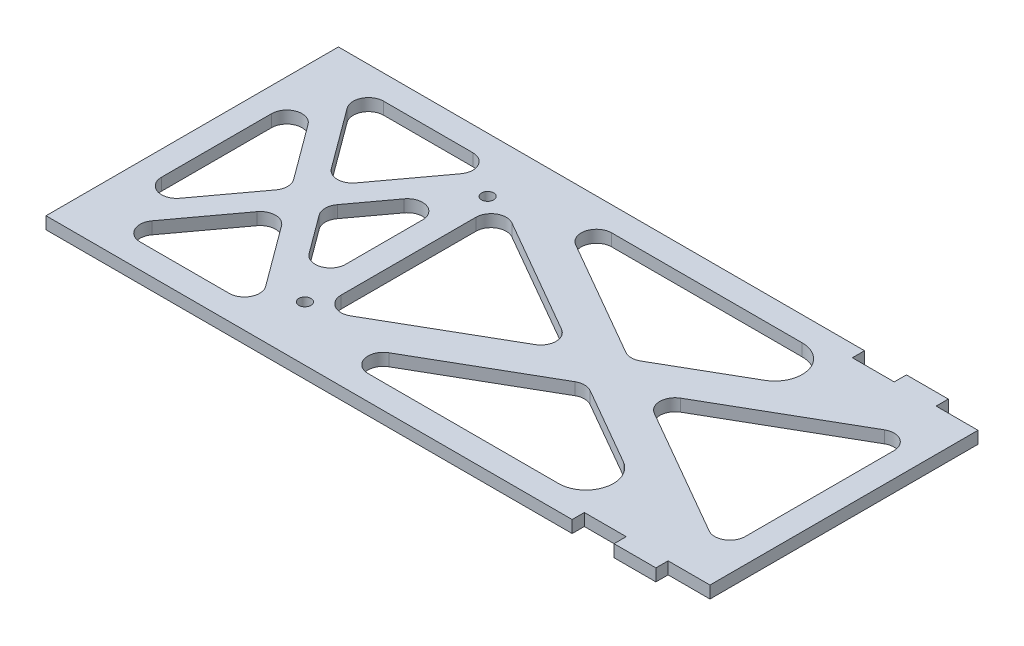
SolidWorks part; units mm, degrees
material "Beech"
ref_plane "Front Plane" through (0, 0, 0) normal (0, 0, 1) x (1, 0, 0)
ref_plane "Top Plane" through (0, 0, 0) normal (0, 1, 0) x (1, 0, 0)
ref_plane "Right Plane" through (0, 0, 0) normal (1, 0, 0) x (0, 0, -1)
sketch "Sketch1" plane through (0, 0, 0) normal (0, 1, 0) x (1, 0, 0)
  line L0 (-50.8, 60.96) -> (-50.8, -60.96) construction
  line L1 (135.89, 60.96) -> (-135.89, 60.96)
  line L2 (135.89, 60.96) -> (135.89, -60.96)
  line L3 (135.89, -60.96) -> (-135.89, -60.96)
  line L4 (-135.89, 60.96) -> (-135.89, -60.96)
  line L5 (135.89, 60.96) -> (-135.89, -60.96) construction
  line L6 (135.89, -60.96) -> (-135.89, 60.96) construction
  line L7 (0, 0) -> (-135.89, 0) construction
  line L8 (125.73, 50.8) -> (-125.73, 50.8)
  line L9 (-125.73, 50.8) -> (-125.73, -50.8)
  line L10 (125.73, -50.8) -> (-125.73, -50.8)
  line L11 (125.73, 50.8) -> (125.73, -50.8)
  line L12 (50.8, 60.96) -> (50.8, -60.96) construction
  line L13 (-125.73, 50.8) -> (-50.8, -50.8) construction
  line L14 (-125.73, -50.8) -> (-50.8, 50.8) construction
  line L15 (-50.8, 50.8) -> (50.8, -50.8) construction
  line L16 (-50.8, -50.8) -> (50.8, 50.8) construction
  line L17 (50.8, 50.8) -> (125.73, -50.8) construction
  line L18 (50.8, -50.8) -> (125.73, 50.8) construction
  line L19 (-125.73, 42.2412) -> (-57.1121, -50.8)
  line L20 (-50.8, 50.8) -> (125.73, -50.8) construction
  line L21 (-50.8, -50.8) -> (125.73, 50.8) construction
  line L22 (-119.4179, -50.8) -> (-53.1582, 39.0437)
  line L23 (-50.9207, 42.0775) -> (-50.8, 42.0081)
  line L24 (-35.524, -50.8) -> (125.73, 42.0081)
  line L25 (-55.88, 60.96) -> (-55.88, -60.96)
  line L26 (-46.999, 57.4043) -> (-45.72, 56.6682)
  line L27 (-119.4179, 50.8) -> (-55.88, -35.3531)
  line L28 (-50.9207, -42.0775) -> (-50.8, -42.0081)
  line L29 (-129.8184, 47.7848) -> (-51.3835, -58.5677) construction
  line L30 (-125.73, -42.2412) -> (-57.1121, 50.8)
  line L31 (-121.6416, 53.8152) -> (-50.2165, -43.0323) construction
  line L32 (-129.8184, -47.7848) -> (-51.3835, 58.5677) construction
  line L33 (-45.72, 60.96) -> (-45.72, -60.96)
  line L34 (-35.524, 50.8) -> (125.73, -42.0081)
  line L35 (-50.2165, -43.0323) -> (51.3835, 58.5677) construction
  line L36 (-51.3835, -58.5677) -> (50.2165, 43.0323) construction
  line L37 (50.2165, 43.0323) -> (121.6416, -53.8152) construction
  line L38 (51.3835, 58.5677) -> (129.8184, -47.7848) construction
  line L39 (-46.999, 57.4043) -> (129.531, -44.1957) construction
  line L40 (-54.601, 44.1957) -> (121.929, -57.4043) construction
  line L41 (-51.3835, 58.5677) -> (50.2165, -43.0323) construction
  line L42 (-50.2165, 43.0323) -> (51.3835, -58.5677) construction
  line L43 (51.3835, -58.5677) -> (129.8184, 47.7848) construction
  line L44 (50.2165, -43.0323) -> (121.6416, 53.8152) construction
  line L45 (-50.9207, 42.0775) -> (-50.2165, 43.0323)
  line L46 (-121.6416, -53.8152) -> (-50.2165, 43.0323) construction
  line L47 (-45.72, 39.0843) -> (110.454, -50.8)
  line L48 (-46.999, -57.4043) -> (129.531, 44.1957) construction
  line L49 (-54.601, -44.1957) -> (121.929, 57.4043) construction
  line L50 (-45.72, -39.0843) -> (110.454, 50.8)
  circle A0 centre (-50.8, 38.1) radius 2.54
  circle A1 centre (-50.8, -38.1) radius 2.54
  point P0 (0, 0)
  dimension "D5" = 5.08
  dimension "D6" = 5.08
  dimension "D1" = 121.92
  dimension "D2" = 271.78
  dimension "D3" = 38.1
  dimension "D4" = 38.1
  dimension "D8" = 50.8
  dimension "tbd gear dim" = 50.8
  dimension "D11" = 5.08
  dimension "D12" = 5.08
  dimension "D7" = 10.16
  dimension "D9" = 7.62
  dimension "D10" = 7.62
  dimension "D13" = 5.08
  dimension "D14" = 5.08
extrude "Boss-Extrude1" add sketch "Sketch1" along normal blind 5.08
fillet "Fillet1" radius 6.35 22 edges at (125.73, 2.54, 42.0081) (125.73, 2.54, -42.0081) (-35.524, 2.54, -50.8) (52.741, 2.54, 0) (37.465, 2.54, -8.7919) (22.189, 2.54, 0) (37.465, 2.54, 8.7919) (-45.72, 2.54, 39.0843) (-35.524, 2.54, 50.8) (-57.1121, 2.54, 50.8) (-45.72, 2.54, -39.0843) (-55.88, 2.54, -35.3531) (-94.5771, 2.54, 0) (-88.265, 2.54, 8.5588) (-81.9529, 2.54, 0) (-119.4179, 2.54, 50.8) (-125.73, 2.54, 42.2412) (-55.88, 2.54, 35.3531) (-88.265, 2.54, -8.5588) (-57.1121, 2.54, -50.8) (-119.4179, 2.54, -50.8) (-125.73, 2.54, -42.2412)
sketch "Sketch3" plane through (0, 5.08, 0) normal (0, 1, 0) x (1, 0, 0)
  line L0 (0, 0) -> (135.89, 0) construction
  line L1 (135.89, 0) -> (135.89, 60.96) construction
  line L2 (135.89, 55.88) -> (66.04, 55.88)
  line L3 (66.04, 55.88) -> (66.04, 60.96)
  line L4 (66.04, 60.96) -> (135.89, 60.96)
  line L5 (100.965, 60.96) -> (100.965, 55.88)
  line L6 (83.5025, 55.88) -> (83.5025, 60.96)
  line L7 (118.4275, 60.96) -> (118.4275, 55.88)
  line L8 (118.4275, -60.96) -> (118.4275, -55.88)
  line L9 (83.5025, -55.88) -> (83.5025, -60.96)
  line L10 (100.965, -60.96) -> (100.965, -55.88)
  line L11 (66.04, -60.96) -> (135.89, -60.96)
  line L12 (66.04, -55.88) -> (66.04, -60.96)
  line L13 (135.89, -55.88) -> (66.04, -55.88)
  line L14 (135.89, 60.96) -> (135.89, 55.88)
  line L15 (135.89, -55.88) -> (135.89, -60.96)
  point P22 (0, 0)
  point P23 (0, 0)
  point P24 (0, 0)
  dimension "D1" = 5.08
  dimension "D2" = 69.85
  dimension "D3" = 135.89
  dimension "D4" = 60.96
  dimension "D5" = 17.4625
  dimension "D6" = 17.4625
extrude "Cut-Extrude2" cut sketch "Sketch3" against normal blind 7.62 contours L6 L2 L5 L4 | L14 L4 L7 L2 | L10 L13 L9 L11 | L15 L13 L8 L11
fillet "Fillet2" radius 11.43 2 edges at (110.454, 2.54, -50.8) (110.454, 2.54, 50.8)
